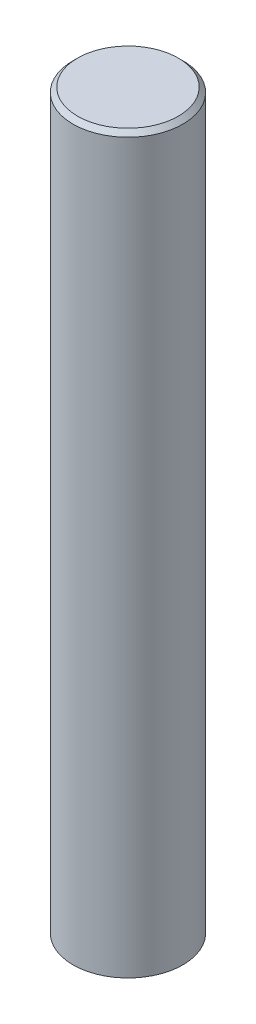
SolidWorks part; units mm, degrees
ref_plane "Front Plane" through (0, 0, 0) normal (0, 0, 1) x (1, 0, 0)
ref_plane "Top Plane" through (0, 0, 0) normal (0, 1, 0) x (1, 0, 0)
ref_plane "Right Plane" through (0, 0, 0) normal (1, 0, 0) x (0, 0, -1)
sketch "Sketch2" plane through (0, 0, 0) normal (0, 1, 0) x (1, 0, 0)
  circle A0 centre (0, 0) radius 12
  dimension "D1" = 24
extrude "Boss-Extrude1" add sketch "Sketch2" along normal blind 160
chamfer "Chamfer1" distance 1 angle 45 1 edges at (0, 160, 12)
